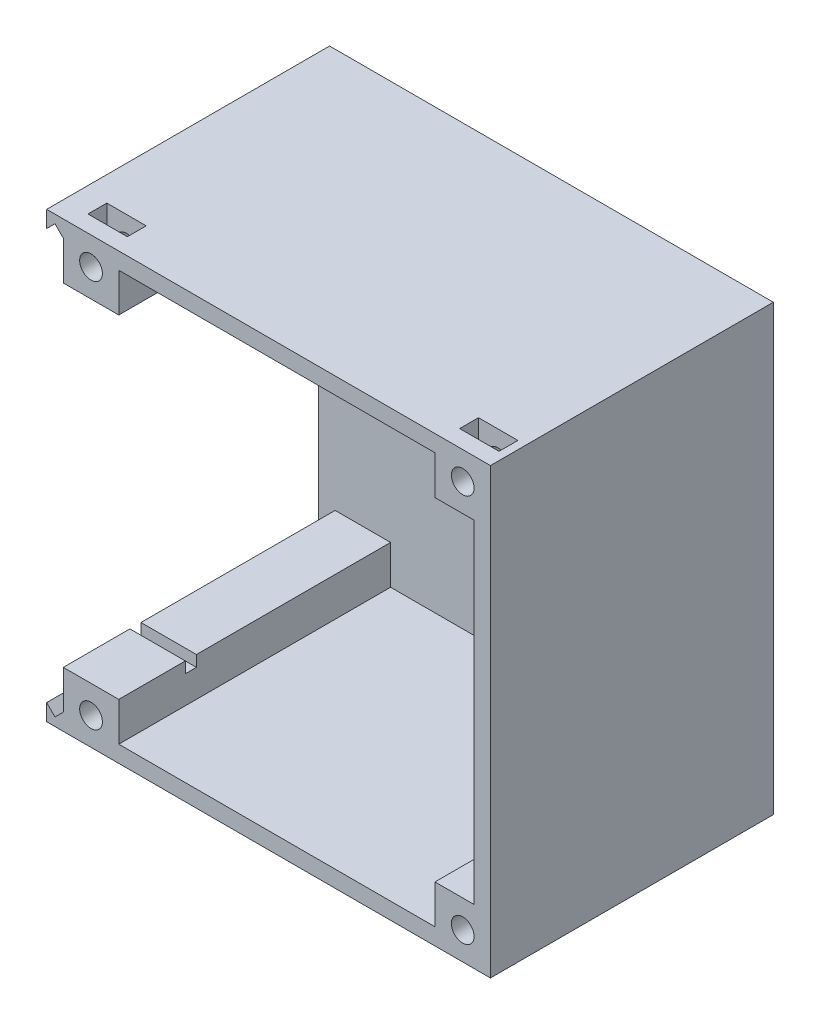
SolidWorks part; units mm, degrees
ref_plane "Plan de face" through (0, 0, 0) normal (0, 0, 1) x (1, 0, 0)
ref_plane "Plan de dessus" through (0, 0, 0) normal (0, 1, 0) x (1, 0, 0)
ref_plane "Plan de droite" through (0, 0, 0) normal (1, 0, 0) x (0, 0, -1)
sketch "Esquisse3" plane through (0, 0, 0) normal (0, 0, 1) x (1, 0, 0)
  line L1 (0, 0) -> (80, 0)
  line L2 (0, 0) -> (0, 80)
  line L3 (0, 80) -> (80, 80)
  line L4 (80, 0) -> (80, 80)
  dimension "D1" = 80
  dimension "D2" = 80
extrude "Boss.-Extru.1" add sketch "Esquisse3" along normal blind 2
sketch "Esquisse6" plane through (0, 0, 2) normal (0, 0, 1) x (1, 0, 0)
  line L0 (0, 0) -> (80, 0)
  line L1 (0, 0) -> (80, 0) construction
  line L2 (80, 0) -> (80, 80)
  line L3 (80, 80) -> (0, 80)
  line L4 (0, 80) -> (0, 77)
  line L5 (0, 80) -> (0, 0) construction
  line L6 (0, 77) -> (1.5, 78.5)
  line L7 (1.5, 78.5) -> (3, 77)
  line L8 (3, 77) -> (3, 70)
  line L9 (3, 70) -> (13, 70)
  line L10 (13, 70) -> (13, 77)
  line L11 (13, 77) -> (70, 77)
  line L12 (70, 77) -> (70, 70)
  line L13 (70, 70) -> (77, 70)
  line L14 (77, 70) -> (77, 10)
  line L15 (77, 10) -> (70, 10)
  line L16 (70, 10) -> (70, 3)
  line L17 (70, 3) -> (13, 3)
  line L18 (13, 3) -> (13, 10)
  line L19 (13, 10) -> (3, 10)
  line L20 (3, 10) -> (3, 3)
  line L21 (3, 3) -> (1.5, 1.5)
  line L22 (1.5, 1.5) -> (0, 3)
  line L23 (0, 3) -> (0, 0)
  dimension "D1" = 3
  dimension "D2" = 3
  dimension "D3" = 3
  dimension "D4" = 45
  dimension "D5" = 90
  dimension "D6" = 3
  dimension "D7" = 3
  dimension "D8" = 3
  dimension "D9" = 3
  dimension "D10" = 45
  dimension "D11" = 90
  dimension "D12" = 3
  dimension "D13" = 3
  dimension "D14" = 10
  dimension "D15" = 10
  dimension "D16" = 10
  dimension "D17" = 10
  dimension "D18" = 10
  dimension "D19" = 10
  dimension "D20" = 10
  dimension "D21" = 10
extrude "Boss.-Extru.2" add sketch "Esquisse6" along normal blind 49
sketch "Esquisse7" plane through (0, 0, 51) normal (0, 0, 1) x (1, 0, 0)
  line L0 (3, 10) -> (3, 3) construction
  line L2 (13, 10) -> (3, 10) construction
  line L3 (70, 10) -> (70, 3) construction
  line L4 (77, 10) -> (70, 10) construction
  line L5 (70, 77) -> (70, 70) construction
  line L6 (70, 70) -> (77, 70) construction
  line L7 (13, 70) -> (13, 77) construction
  line L8 (3, 70) -> (13, 70) construction
  circle A0 centre (8, 75) radius 2.05
  circle A1 centre (8, 5) radius 2.05
  circle A2 centre (75, 5) radius 2.05
  circle A3 centre (75, 75) radius 2.05
  dimension "D1" = 4.1
  dimension "D2" = 4.1
  dimension "D3" = 4.1
  dimension "D4" = 4.1
  dimension "D5" = 5
  dimension "D6" = 5
  dimension "D7" = 5
  dimension "D8" = 5
  dimension "D9" = 5
  dimension "D10" = 5
  dimension "D11" = 5
  dimension "D12" = 5
extrude "Enlèv. mat.-Extru.1" cut sketch "Esquisse7" against normal blind 30
sketch "Esquisse8" plane through (0, 0, 0) normal (0, -1, 0) x (1, 0, 0)
  line L0 (0, 51) -> (0, 0) construction
  line L1 (4.45, 48) -> (11.55, 48)
  line L2 (4.45, 48) -> (4.45, 44.6)
  line L3 (4.45, 44.6) -> (11.55, 44.6)
  line L4 (11.55, 48) -> (11.55, 44.6)
  line L5 (0, 51) -> (80, 51) construction
  line L6 (80, 51) -> (80, 0) construction
  line L7 (71.45, 48) -> (78.55, 48)
  line L8 (71.45, 48) -> (71.45, 44.6)
  line L9 (71.45, 44.6) -> (78.55, 44.6)
  line L10 (78.55, 48) -> (78.55, 44.6)
  dimension "D1" = 7.1
  dimension "D2" = 3.4
  dimension "D3" = 4.45
  dimension "D4" = 3
  dimension "D5" = 3.4
  dimension "D6" = 3
  dimension "D7" = 1.45
  dimension "D8" = 7.1
extrude "Enlèv. mat.-Extru.2" cut sketch "Esquisse8" against normal blind 9
sketch "Esquisse9" plane through (0, 80, 0) normal (0, 1, 0) x (1, 0, 0)
  line L0 (80, -51) -> (0, -51) construction
  line L1 (78.55, -48) -> (71.45, -48)
  line L2 (78.55, -48) -> (78.55, -44.6)
  line L3 (78.55, -44.6) -> (71.45, -44.6)
  line L4 (71.45, -48) -> (71.45, -44.6)
  line L5 (11.55, -48) -> (4.45, -48)
  line L6 (11.55, -48) -> (11.55, -44.6)
  line L7 (11.55, -44.6) -> (4.45, -44.6)
  line L8 (4.45, -48) -> (4.45, -44.6)
  line L9 (80, -51) -> (80, 0) construction
  line L10 (0, -51) -> (0, 0) construction
  dimension "D1" = 7.1
  dimension "D2" = 7.1
  dimension "D3" = 3.4
  dimension "D4" = 3.4
  dimension "D5" = 3
  dimension "D6" = 3
  dimension "D7" = 1.45
  dimension "D8" = 4.45
extrude "Enlèv. mat.-Extru.3" cut sketch "Esquisse9" against normal blind 9
sketch "Esquisse10" plane through (3, 0, 0) normal (-1, 0, 0) x (0, 0, 1)
  line L0 (51, 70) -> (2, 70) construction
  line L1 (39, 72) -> (37, 72)
  line L2 (39, 72) -> (39, 70)
  line L3 (39, 70) -> (37, 70)
  line L4 (37, 72) -> (37, 70)
  line L5 (51, 10) -> (2, 10) construction
  line L6 (39, 10) -> (37, 10)
  line L7 (39, 10) -> (39, 8)
  line L8 (39, 8) -> (37, 8)
  line L9 (37, 10) -> (37, 8)
  line L10 (51, 10) -> (51, 3) construction
  line L11 (51, 77) -> (51, 70) construction
  dimension "D1" = 2
  dimension "D2" = 2
  dimension "D3" = 2
  dimension "D4" = 2
  dimension "D5" = 14
  dimension "D6" = 14
extrude "Enlèv. mat.-Extru.4" cut sketch "Esquisse10" against normal blind 74
